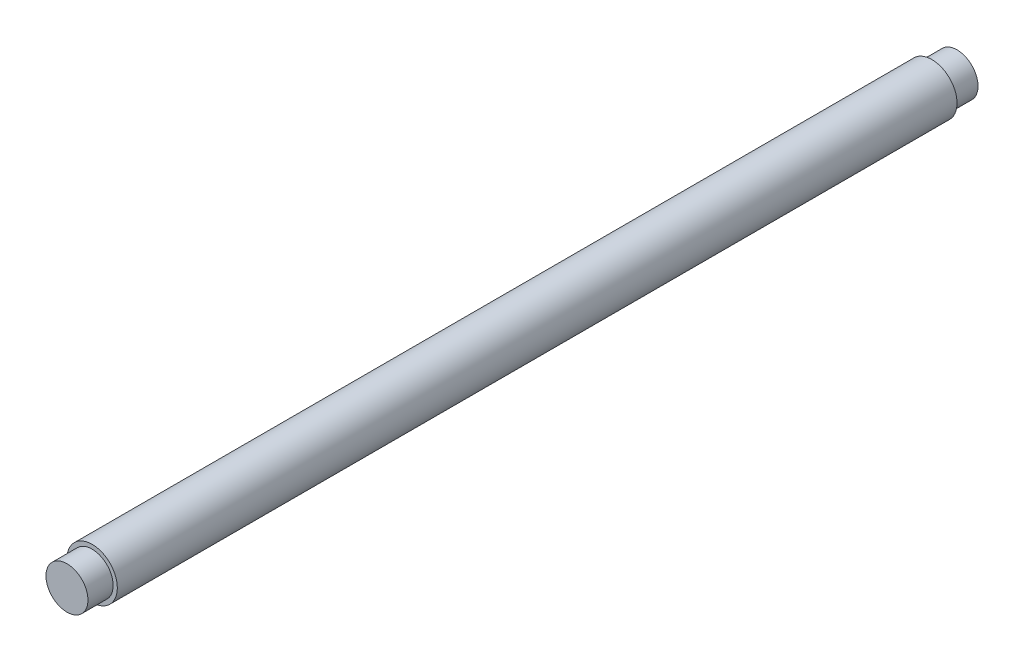
SolidWorks part; units mm, degrees
ref_plane "Front Plane" through (0, 0, 0) normal (0, 0, 1) x (1, 0, 0)
ref_plane "Top Plane" through (0, 0, 0) normal (0, 1, 0) x (1, 0, 0)
ref_plane "Right Plane" through (0, 0, 0) normal (1, 0, 0) x (0, 0, -1)
sketch "Sketch1" plane through (0, 0, 0) normal (1, 0, 0) x (0, 0, -1)
  line L0 (-75, 0) -> (75, 0) construction
  line L1 (0, -3) -> (0, 3) construction
  point P0 (-59, 0)
  point P3 (59, 0)
  point P4 (0, 0)
  point P8 (0, 0)
  dimension "Diameter" = 6
  dimension "Length" = 150
  dimension "Break View Space" = 16
  dimension "D2" = 16
sketch "Sketch2" plane through (0, 0, 0) normal (0, 0, 1) x (1, 0, 0)
  circle A0 centre (0, 0) radius 3
extrude "Boss-Extrude1" add sketch "Sketch2" along normal up to vertex (75 mm away) and the other way up to vertex (75 mm away) up to point (0, 0, 75) other way up to point (0, 0, -75)
chamfer "Chamfer1" distance 0.12 angle 45 2 edges at (3, 0, -75) (3, 0, 75)
sketch "Sketch3" plane through (0, 0, 0) normal (0, 0, 1) x (1, 0, 0)
  circle A0 centre (0, 0) radius 3 construction
  circle A1 centre (0, 0) radius 3
  dimension "D1" = 6
sketch "Sketch4" plane through (0, 0, -75) normal (0, 0, -1) x (-1, 0, 0)
  circle A0 centre (0, 0) radius 3 construction
  circle A1 centre (0, 0) radius 3
extrude "Cut-Extrude1" cut sketch "Sketch4" against normal offset from surface (44 mm away) 106 up to face at (2.88, 0, 75)
sketch "Sketch5" plane through (0, 0, -31) normal (0, 0, -1) x (-1, 0, 0)
  circle A0 centre (0, 0) radius 2.5
  dimension "D1" = 5
extrude "Cut-Extrude2" cut sketch "Sketch5" against normal blind 3 flip side to cut
sketch "Sketch6" plane through (0, 0, 75) normal (0, 0, 1) x (1, 0, 0)
  circle A0 centre (0, 0) radius 2.5
  dimension "D1" = 5
extrude "Cut-Extrude3" cut sketch "Sketch6" against normal blind 3 flip side to cut
equation "\"D1@Chamfer1\"=\"Diameter@Sketch1\"*.02"
equation "\"D2@Sketch1\" = \"Break View Space@Sketch1\""
